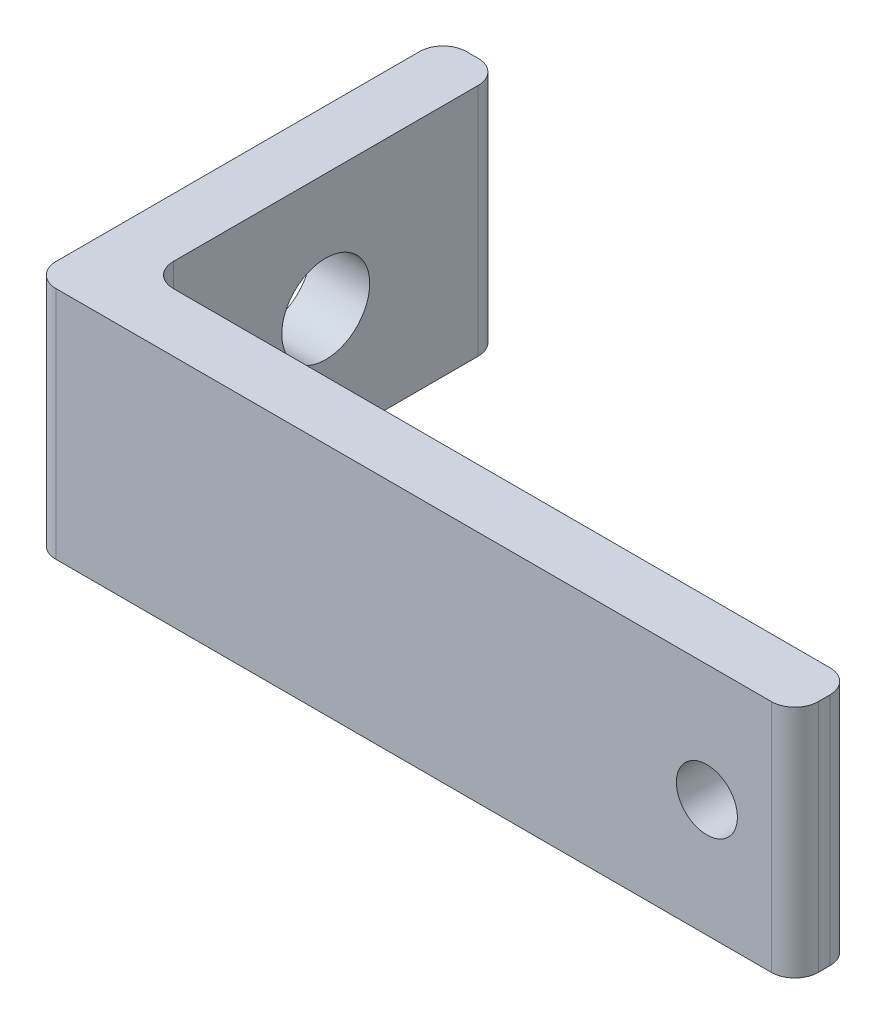
SolidWorks part; units mm, degrees
ref_plane "Front Plane" through (0, 0, 0) normal (0, 0, 1) x (1, 0, 0)
ref_plane "Top Plane" through (0, 0, 0) normal (0, 1, 0) x (1, 0, 0)
ref_plane "Right Plane" through (0, 0, 0) normal (1, 0, 0) x (0, 0, -1)
sketch "Sketch1" plane through (0, 0, 0) normal (0, 1, 0) x (1, 0, 0)
  line L1 (0, 0) -> (6.35, 0)
  line L2 (0, 0) -> (0, 44.45)
  line L3 (0, 44.45) -> (6.35, 44.45)
  line L4 (6.35, 0) -> (6.35, 44.45)
  line L5 (0, 0) -> (82.55, 0)
  line L6 (0, 0) -> (0, 6.35)
  line L7 (0, 6.35) -> (82.55, 6.35)
  line L8 (82.55, 0) -> (82.55, 6.35)
  dimension "D1" = 6.35
  dimension "D2" = 44.45
  dimension "D3" = 82.55
  dimension "D4" = 6.35
extrude "Boss-Extrude1" add sketch "Sketch1" along normal blind 25.4 contours L2 L7 L4 L3 | L7 L2 L1 L4 | L5 L8 L7 L4
sketch "Sketch2" plane through (0, 0, -6.35) normal (0, 0, -1) x (-1, 0, 0)
  line L0 (-82.55, 25.4) -> (-82.55, 0) construction
  circle A0 centre (-73.025, 12.7) radius 3.302
  dimension "D1" = 6.604
  dimension "D2" = 9.525
extrude "Cut-Extrude1" cut sketch "Sketch2" against normal through all
sketch "Sketch3" plane through (6.35, 0, 0) normal (1, 0, 0) x (0, 0, -1)
  line L0 (44.45, 25.4) -> (44.45, 0) construction
  circle A0 centre (25.4, 12.7) radius 4.7625
  dimension "D1" = 19.05
  dimension "D2" = 9.525
extrude "Cut-Extrude2" cut sketch "Sketch3" against normal through all
fillet "Fillet1" radius 2.54 6 edges at (0, 12.7, 0) (6.35, 12.7, -44.45) (82.55, 12.7, -6.35) (6.35, 12.7, -6.35) (0, 12.7, -44.45) (82.55, 12.7, 0)
